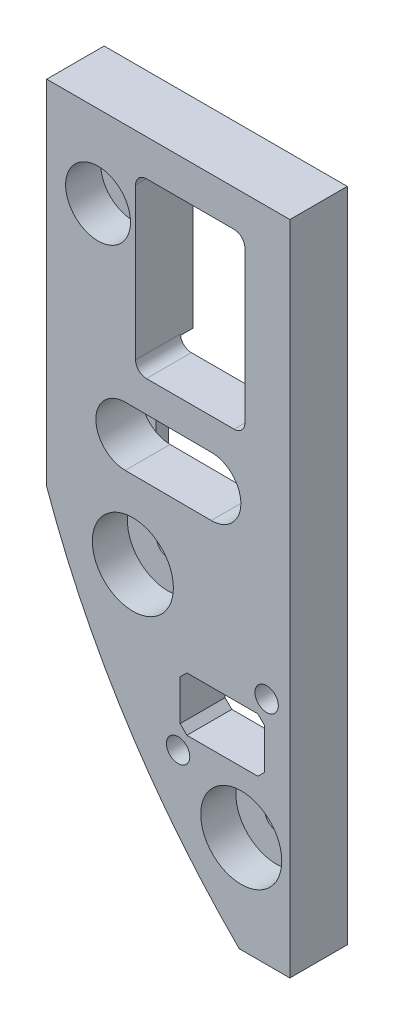
SolidWorks part; units mm, degrees
material "PET"
ref_plane "Front" through (0, 0, 0) normal (0, 0, 1) x (1, 0, 0)
ref_plane "Top" through (0, 0, 0) normal (0, 1, 0) x (1, 0, 0)
ref_plane "Right" through (0, 0, 0) normal (1, 0, 0) x (0, 0, -1)
sketch "Sketch1" plane through (0, 0, 0) normal (0, 0, 1) x (1, 0, 0)
  line L0 (-1.8976, -121.9236) -> (-1.8976, -95.5711)
  line L1 (-1.8976, -95.5711) -> (-12.1665, -95.5711)
  line L2 (-12.1665, -95.5711) -> (-16.929, -90.8086)
  line L3 (-16.929, -90.8086) -> (-23.4876, -90.8086)
  line L4 (0, -17.78) -> (-45.72, -17.78)
  line L5 (-45.72, -17.78) -> (-45.72, -84.1375)
  line L6 (-9.525, -141.2875) -> (0, -141.2875)
  line L7 (0, -141.2875) -> (0, -17.78)
  line L8 (0, -17.78) -> (-45.72, -17.78)
  line L9 (-45.72, -17.78) -> (-45.72, -84.1375)
  line L10 (-9.525, -141.2875) -> (0, -141.2875)
  line L11 (0, -141.2875) -> (0, -17.78)
  line L12 (-23.4876, -90.8086) -> (-23.4876, -117.1611)
  line L13 (-23.4876, -117.1611) -> (-13.2186, -117.1611)
  line L14 (-13.2186, -117.1611) -> (-9.5028, -120.877)
  line L15 (-7.2795, -121.9236) -> (-1.8976, -121.9236)
  line L16 (-32.385, -80.4545) -> (-9.525, -80.4545)
  line L17 (-9.525, -80.4545) -> (-9.525, -76.6445)
  line L18 (-9.525, -76.6445) -> (-13.335, -72.8345)
  line L19 (-13.335, -72.8345) -> (-13.335, -56.642)
  line L20 (-13.335, -56.642) -> (-36.195, -56.642)
  line L21 (-36.195, -56.642) -> (-36.195, -60.452)
  line L22 (-36.195, -60.452) -> (-32.385, -64.262)
  line L23 (-32.385, -64.262) -> (-32.385, -80.4545)
  line L24 (-32.385, -80.4545) -> (-9.525, -80.4545) construction
  line L25 (-9.525, -80.4545) -> (-9.525, -76.6445) construction
  line L26 (-9.525, -76.6445) -> (-13.335, -72.8345) construction
  line L27 (-13.335, -72.8345) -> (-13.335, -56.642) construction
  line L28 (-13.335, -56.642) -> (-36.195, -56.642) construction
  line L29 (-36.195, -56.642) -> (-36.195, -60.452) construction
  line L30 (-36.195, -60.452) -> (-32.385, -64.262) construction
  line L31 (-32.385, -64.262) -> (-32.385, -80.4545) construction
  line L32 (-3.1676, -120.6536) -> (-3.1676, -96.8411)
  line L33 (-3.1676, -96.8411) -> (-12.6926, -96.8411)
  line L34 (-12.6926, -96.8411) -> (-17.4551, -92.0786)
  line L35 (-17.4551, -92.0786) -> (-22.2176, -92.0786)
  line L36 (-22.2176, -92.0786) -> (-22.2176, -115.8911)
  line L37 (-22.2176, -115.8911) -> (-12.6926, -115.8911)
  line L38 (-12.6926, -115.8911) -> (-7.9301, -120.6536)
  line L39 (-7.9301, -120.6536) -> (-3.1676, -120.6536)
  line L40 (-3.1676, -120.6536) -> (-3.1676, -96.8411) construction
  line L41 (-3.1676, -96.8411) -> (-12.6926, -96.8411) construction
  line L42 (-12.6926, -96.8411) -> (-17.4551, -92.0786) construction
  line L43 (-17.4551, -92.0786) -> (-22.2176, -92.0786) construction
  line L44 (-22.2176, -92.0786) -> (-22.2176, -115.8911) construction
  line L45 (-22.2176, -115.8911) -> (-12.6926, -115.8911) construction
  line L46 (-12.6926, -115.8911) -> (-7.9301, -120.6536) construction
  line L47 (-7.9301, -120.6536) -> (-3.1676, -120.6536) construction
  line L48 (-33.655, -81.7245) -> (-8.255, -81.7245)
  line L49 (-8.255, -81.7245) -> (-8.255, -76.1184)
  line L50 (-8.255, -76.1184) -> (-12.065, -72.3084)
  line L51 (-12.065, -72.3084) -> (-12.065, -57.1627)
  line L52 (-29.0068, -55.372) -> (-37.465, -55.372)
  line L53 (-37.465, -55.372) -> (-37.465, -60.9781)
  line L54 (-37.465, -60.9781) -> (-33.655, -64.7881)
  line L55 (-33.655, -64.7881) -> (-33.655, -81.7245)
  line L80 (-8.4582, -55.1307) -> (-8.4582, -26.6573)
  line L81 (-26.9748, -57.1627) -> (-10.4902, -57.1627)
  line L82 (-29.0068, -26.6573) -> (-29.0068, -55.1307)
  line L83 (-10.4902, -24.6253) -> (-26.9748, -24.6253)
  line L84 (-8.4582, -55.1307) -> (-8.4582, -26.6573)
  line L86 (-29.0068, -26.6573) -> (-29.0068, -55.372)
  line L87 (-10.4902, -24.6253) -> (-26.9748, -24.6253)
  line L2565 (-12.065, -72.3084) -> (-12.065, -55.372) construction
  line L2566 (-12.065, -55.372) -> (-37.465, -55.372) construction
  line L2567 (-12.065, -57.1627) -> (-10.4902, -57.1627)
  line L2568 (-13.2186, -117.1611) -> (-8.4561, -121.9236) construction
  line L2569 (-8.4561, -121.9236) -> (-1.8976, -121.9236) construction
  circle A1 centre (-36.1315, -33.274) radius 2.1526
  circle A2 centre (-36.1315, -33.274) radius 2.1526
  circle A3 centre (-29.5275, -88.7095) radius 2.1526
  circle A4 centre (-29.5275, -88.7095) radius 2.1527
  circle A5 centre (-9.144, -122.9995) radius 2.1526
  arc A6 (-9.5028, -120.877) -> (-7.2795, -121.9236) centre (-9.144, -122.9995) ccw
  arc A7 (-45.72, -84.1375) -> (-9.525, -141.2875) centre (97.9169, -33.2042) ccw
  arc A8 (-45.72, -84.1375) -> (-9.525, -141.2875) centre (97.9169, -33.2042) ccw
  arc A16 (-8.4582, -26.6573) -> (-10.4902, -24.6253) centre (-10.4902, -26.6573) ccw
  arc A17 (-10.4902, -57.1627) -> (-8.4582, -55.1307) centre (-10.4902, -55.1307) ccw
  arc A18 (-29.0068, -55.1307) -> (-26.9748, -57.1627) centre (-26.9748, -55.1307) ccw
  arc A19 (-26.9748, -24.6253) -> (-29.0068, -26.6573) centre (-26.9748, -26.6573) ccw
  arc A20 (-8.4582, -26.6573) -> (-10.4902, -24.6253) centre (-10.4902, -26.6573) ccw
  arc A21 (-10.4902, -57.1627) -> (-8.4582, -55.1307) centre (-10.4902, -55.1307) ccw
  arc A23 (-26.9748, -24.6253) -> (-29.0068, -26.6573) centre (-26.9748, -26.6573) ccw
  dimension "D1" = 0
  dimension "D2" = 0
  dimension "D3" = 0
  dimension "D4" = 0
  dimension "D5" = 0
  dimension "D6" = 0
  dimension "D7" = 1.27
  dimension "D8" = 1.27
  dimension "D9" = 1.27
extrude "Boss-Extrude1" add sketch "Sketch1" along normal offset from surface (2.3495 mm away) 0.762 contours L8 L9 A8 L10 L11
sketch "Sketch2" plane through (0, 0, 2.3495) normal (0, 0, 1) x (1, 0, 0)
  line L0 (-12.6926, -105.7961) -> (-12.6926, -106.9361) construction
  line L4 (-9.525, -141.2875) -> (0, -141.2875)
  line L5 (0, -141.2875) -> (0, -17.78)
  line L6 (0, -17.78) -> (-45.72, -17.78)
  line L7 (-45.72, -17.78) -> (-45.72, -84.1375)
  line L8 (-9.525, -141.2875) -> (0, -141.2875)
  line L9 (0, -141.2875) -> (0, -17.78)
  line L10 (0, -17.78) -> (-45.72, -17.78)
  line L11 (-45.72, -17.78) -> (-45.72, -84.1375)
  line L13 (-4.7551, -111.4461) -> (-20.6301, -111.4461)
  line L14 (-4.7551, -111.4461) -> (-4.7551, -101.2861)
  line L15 (-4.7551, -101.2861) -> (-20.6301, -101.2861)
  line L16 (-20.6301, -111.4461) -> (-20.6301, -101.2861)
  line L17 (-4.7551, -111.4461) -> (-20.6301, -101.2861) construction
  line L18 (-4.7551, -101.2861) -> (-20.6301, -111.4461) construction
  line L19 (-22.8475, -67.6357) -> (-22.8475, -69.5407) construction
  line L20 (-22.53, -67.6357) -> (-23.165, -67.6357) construction
  line L21 (-23.165, -69.5407) -> (-22.53, -69.5407) construction
  line L22 (-14.7705, -68.6282) -> (-30.9245, -68.5483) construction
  line L23 (-14.798, -74.1844) -> (-30.952, -74.1044)
  line L24 (-14.743, -63.0721) -> (-30.897, -62.9921)
  line L33 (-8.4582, -55.1307) -> (-8.4582, -26.6573)
  line L34 (-26.9748, -57.1627) -> (-10.4902, -57.1627)
  line L35 (-29.0068, -26.6573) -> (-29.0068, -55.1307)
  line L36 (-10.4902, -24.6253) -> (-26.9748, -24.6253)
  line L37 (-8.4582, -55.1307) -> (-8.4582, -26.6573)
  line L38 (-26.9748, -57.1627) -> (-10.4902, -57.1627)
  line L39 (-29.0068, -26.6573) -> (-29.0068, -55.1307)
  line L40 (-10.4902, -24.6253) -> (-26.9748, -24.6253)
  circle A0 centre (-9.144, -122.9995) radius 2.1526 construction
  arc A1 (-45.72, -84.1375) -> (-9.525, -141.2875) centre (97.9169, -33.2042) ccw
  arc A2 (-45.72, -84.1375) -> (-9.525, -141.2875) centre (97.9169, -33.2042) ccw
  circle A3 centre (-9.144, -122.9995) radius 2.1526
  circle A4 centre (-29.5275, -88.7095) radius 2.1526 construction
  circle A5 centre (-29.5275, -88.7095) radius 2.1527
  circle A10 centre (-21.016, -114.6896) radius 1.4336 construction
  circle A11 centre (-21.016, -114.6896) radius 1.4336 construction
  circle A12 centre (-4.3691, -98.0426) radius 1.4336 construction
  circle A13 centre (-4.3691, -98.0426) radius 1.4336 construction
  circle A15 centre (-30.9245, -68.5483) radius 1.4336 construction
  circle A17 centre (-30.9245, -68.5483) radius 1.4336 construction
  circle A18 centre (-21.016, -114.6896) radius 2.1956
  circle A19 centre (-4.3691, -98.0426) radius 2.1956
  circle A20 centre (-30.9245, -68.5483) radius 2.1956 construction
  arc A22 (-14.798, -74.1844) -> (-14.743, -63.0721) centre (-14.7705, -68.6282) ccw
  arc A23 (-30.897, -62.9921) -> (-30.952, -74.1044) centre (-30.9245, -68.5483) ccw
  arc A32 (-8.4582, -26.6573) -> (-10.4902, -24.6253) centre (-10.4902, -26.6573) ccw
  arc A33 (-10.4902, -57.1627) -> (-8.4582, -55.1307) centre (-10.4902, -55.1307) ccw
  arc A34 (-29.0068, -55.1307) -> (-26.9748, -57.1627) centre (-26.9748, -55.1307) ccw
  arc A35 (-26.9748, -24.6253) -> (-29.0068, -26.6573) centre (-26.9748, -26.6573) ccw
  arc A36 (-8.4582, -26.6573) -> (-10.4902, -24.6253) centre (-10.4902, -26.6573) ccw
  arc A37 (-10.4902, -57.1627) -> (-8.4582, -55.1307) centre (-10.4902, -55.1307) ccw
  arc A38 (-29.0068, -55.1307) -> (-26.9748, -57.1627) centre (-26.9748, -55.1307) ccw
  arc A39 (-26.9748, -24.6253) -> (-29.0068, -26.6573) centre (-26.9748, -26.6573) ccw
  circle A472 centre (-36.1315, -33.274) radius 2.1526 construction
  circle A473 centre (-36.1315, -33.274) radius 2.1526
  point P19 (-22.8475, -68.5882)
  point P32 (-12.6926, -106.3661)
  dimension "D3" = 15.875
  dimension "D4" = 10.16
  dimension "D5" = 11.1125
  dimension "D6" = 1.27
  dimension "D1" = 0
  dimension "D2" = 0.762
extrude "Boss-Extrude2" add sketch "Sketch2" along normal up to surface (8.4455 mm away)
sketch "Sketch3" plane through (0, 0, 2.3495) normal (0, 0, -1) x (-1, 0, 0)
  circle A0 centre (34.29, -58.547) radius 1.3525 construction
  circle A1 centre (11.43, -78.5495) radius 1.3525 construction
  circle A2 centre (5.5488, -118.2724) radius 1.3525 construction
  circle A3 centre (19.8363, -94.4599) radius 1.3525 construction
  circle A4 centre (34.29, -58.547) radius 1.3525 construction
  circle A5 centre (11.43, -78.5495) radius 1.3525 construction
  circle A6 centre (5.5488, -118.2724) radius 1.3525 construction
  circle A7 centre (19.8363, -94.4599) radius 1.3525 construction
  circle A8 centre (34.29, -58.547) radius 1.2255
  circle A9 centre (11.43, -78.5495) radius 1.2255
  circle A10 centre (5.5488, -118.2724) radius 1.2255
  circle A11 centre (19.8363, -94.4599) radius 1.2255
  dimension "D1" = 0.127
extrude "Boss-Extrude3" add sketch "Sketch3" along normal blind 2.159
chamfer "Chamfer1" distance 0.254 angle 45 4 edges at (-35.5155, -58.547, 0.1905) (-12.6555, -78.5495, 0.1905) (-21.0619, -94.4599, 0.1905) (-6.7744, -118.2724, 0.1905)
chamfer "Chamfer2" distance 1.27 angle 45 4 edges at (-20.6301, -101.2861, 6.5723) (-20.6301, -111.4461, 6.5723) (-4.7551, -111.4461, 6.5723) (-4.7551, -101.2861, 6.5723)
sketch "Sketch5" plane through (0, 0, 10.795) normal (0, 0, 1) x (1, 0, 0)
  circle A0 centre (-9.144, -122.9995) radius 6.35 construction
  circle A1 centre (-29.5275, -88.7095) radius 6.35 construction
  circle A2 centre (-36.068, -33.2105) radius 4.826 construction
  circle A6 centre (-9.144, -122.9995) radius 6.35 construction
  circle A7 centre (-29.5275, -88.7095) radius 6.35 construction
  circle A8 centre (-36.068, -33.2105) radius 4.826 construction
  circle A9 centre (-9.144, -122.9995) radius 7.62
  circle A10 centre (-29.5275, -88.7095) radius 7.62
  circle A11 centre (-36.068, -33.2105) radius 6.096
  dimension "D1" = 1.27
extrude "Cut-Extrude1" cut sketch "Sketch5" against normal blind 6.604
